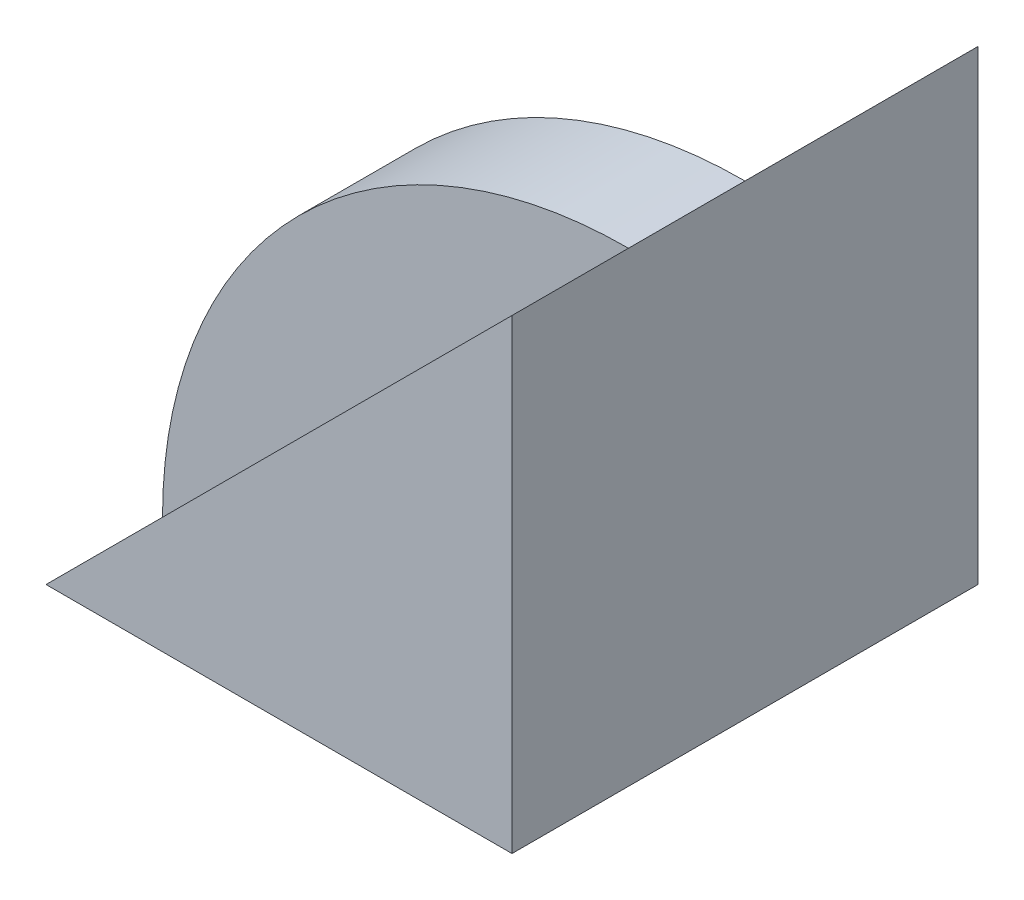
SolidWorks part; units mm, degrees
ref_plane "Front Plane" through (0, 0, 0) normal (0, 0, 1) x (1, 0, 0)
ref_plane "Top Plane" through (0, 0, 0) normal (0, 1, 0) x (1, 0, 0)
ref_plane "Right Plane" through (0, 0, 0) normal (1, 0, 0) x (0, 0, -1)
sketch "Sketch1" plane through (0, 0, 0) normal (0, 0, 1) x (1, 0, 0)
  line L0 (0, 0) -> (-40, 0)
  line L1 (-40, 0) -> (0, 40)
  line L2 (0, 40) -> (0, 0)
  dimension "D1" = 40
  dimension "D2" = 40
extrude "Boss-Extrude1" add sketch "Sketch1" along normal blind 10
sketch "Sketch2" plane through (0, 0, 0) normal (0, 0, -1) x (-1, 0, 0)
  line L0 (0, 40) -> (40, 0) construction
  line L1 (0, 40) -> (0, 0)
  line L2 (0, 0) -> (40, 0)
  arc A0 (40, 0) -> (0, 40) centre (0, 0) ccw
extrude "Boss-Extrude2" add sketch "Sketch2" along normal blind 10
sketch "Sketch3" plane through (0, 0, -10) normal (0, 0, -1) x (-1, 0, 0)
  line L0 (0, 40) -> (0, 0)
  line L1 (0, 0) -> (40, 0)
  line L2 (0, 0) -> (40, 0) construction
  line L3 (40, 0) -> (0, 40)
  dimension "D1" = 40
extrude "Boss-Extrude4" add sketch "Sketch3" along normal blind 20
sketch "Sketch5" plane through (0, 0, 0) normal (0, -1, 0) x (1, 0, 0)
  line L0 (0, -30) -> (-40, -10)
  line L1 (-40, -10) -> (-40, -30)
  line L2 (-40, -30) -> (0, -30)
extrude "Cut-Extrude3" cut sketch "Sketch5" against normal blind 57
